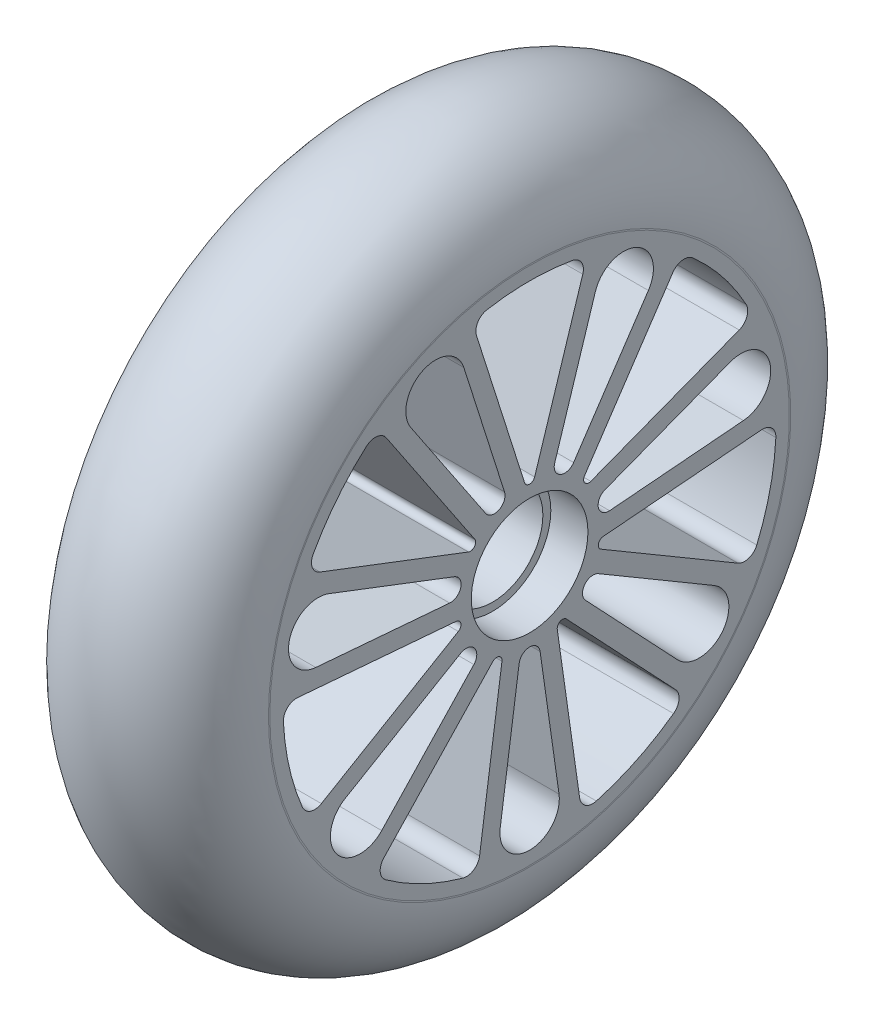
SolidWorks part; units mm, degrees
ref_plane "Front Plane" through (0, 0, 0) normal (0, 0, 1) x (1, 0, 0)
ref_plane "Top Plane" through (0, 0, 0) normal (0, 1, 0) x (1, 0, 0)
ref_plane "Right Plane" through (0, 0, 0) normal (1, 0, 0) x (0, 0, -1)
sketch "Sketch2" plane through (0, 0, 0) normal (0, 0, 1) x (1, 0, 0)
  line L0 (0, -49) -> (0, 49) construction
  line L1 (-14.0194, 46.0581) -> (14.0194, 46.0581)
  line L2 (17.4377, 49.2586) -> (17.4396, 49)
  line L3 (-19.6452, 0) -> (17.4396, 0) construction
  arc A0 (-17.4396, 49) -> (17.4377, 49.2586) centre (0, 49) cw
  arc A1 (-17.4396, 49) -> (-14.0194, 46.0581) centre (-17.4396, 45.5408) cw
  arc A2 (17.4396, 49) -> (14.0194, 46.0581) centre (17.4396, 45.5408) ccw
  point P3 (0, 0)
  point P13 (0, 46.0581)
  dimension "D1" = 98
revolve "Revolve1" add sketch "Sketch2" angle 360 about L3
sketch "Sketch4" plane through (0, 0, 0) normal (0, 0, 1) x (1, 0, 0)
  line L0 (-14.0194, 46.0581) -> (14.0194, 46.0581) construction
  line L1 (-14.0194, 46.0581) -> (14.0194, 46.0581)
  line L2 (-17.4396, 0) -> (-17.4396, 49)
  line L3 (-17.4396, 49) -> (-17.4396, -49) construction
  line L4 (-17.4396, 0) -> (17.4396, 0)
  line L5 (17.4396, 0) -> (17.4396, 49)
  arc A0 (17.4396, 49) -> (14.0194, 46.0581) centre (17.4396, 45.5408) ccw construction
  arc A1 (-14.0194, 46.0581) -> (-17.4396, 49) centre (-17.4396, 45.5408) ccw construction
  arc A2 (17.4396, 49) -> (14.0194, 46.0581) centre (17.4396, 45.5408) ccw
  arc A3 (-14.0194, 46.0581) -> (-17.4396, 49) centre (-17.4396, 45.5408) ccw
revolve "Revolve2" add sketch "Sketch4" angle 360 about L4
sketch "Sketch5" plane through (17.4396, 0, 0) normal (1, 0, 0) x (0, 0, -1)
  line L0 (0, 49.2586) -> (0, -49.2586) construction
  line L1 (-49, 0) -> (49.2586, 0) construction
  circle A0 centre (0, 0) radius 49.2586 construction
  circle A1 centre (0, 0) radius 49 construction
  circle A2 centre (0, 0) radius 11
  dimension "D1" = 22
extrude "Cut-Extrude1" cut sketch "Sketch5" against normal blind 7
mirror "Mirror1" about plane through (0, 0, 0) normal (1, 0, 0) of "Cut-Extrude1"
sketch "Sketch6" plane through (10.4396, 0, 0) normal (1, 0, 0) x (0, 0, -1)
  circle A0 centre (0, 0) radius 9.5
  circle A1 centre (0, 0) radius 11 construction
  dimension "D1" = 1.5
extrude "Cut-Extrude2" cut sketch "Sketch6" against normal through all both and the other way through all
sketch "Sketch7" plane through (17.4396, 0, 0) normal (1, 0, 0) x (0, 0, -1)
  line L0 (0, 0) -> (0, 66.4396) construction
  line L1 (0.9531, 14.0016) -> (10.026, 42.5745)
  line L2 (-0.9531, 14.0016) -> (-10.026, 42.5745)
  line L3 (10.3526, 9.475) -> (27.035, 34.3834)
  line L4 (11.5411, 7.9847) -> (39.5371, 18.7061)
  line L5 (13.8626, -2.1864) -> (43.738, 0.3009)
  line L6 (13.4384, -4.0449) -> (39.276, -19.2483)
  line L7 (6.9338, -12.2014) -> (27.5055, -34.0082)
  line L8 (5.2163, -13.0285) -> (9.4393, -42.7084)
  line L9 (-5.2163, -13.0285) -> (-9.4393, -42.7084)
  line L10 (-6.9338, -12.2014) -> (-27.5055, -34.0082)
  line L11 (-13.4384, -4.0449) -> (-39.276, -19.2483)
  line L12 (-13.8626, -2.1864) -> (-43.738, 0.3009)
  line L13 (-11.5411, 7.9847) -> (-39.5371, 18.7061)
  line L14 (-10.3526, 9.475) -> (-27.035, 34.3834)
  line L15 (10.026, 42.5745) -> (27.035, 34.3834) construction
  line L16 (0.9531, 14.0016) -> (10.3526, 9.475) construction
  line L17 (5.6529, 11.7383) -> (18.5305, 38.4789) construction
  line L18 (18.5305, 38.4789) -> (20.1756, 41.8951) construction
  line L19 (4.7346, 14.3927) -> (12.4028, 38.542)
  line L20 (8.3007, 12.6753) -> (22.4003, 33.7274)
  line L21 (14.2046, 5.2721) -> (37.8663, 14.3337)
  line L22 (15.0854, 1.4132) -> (40.3355, 3.5154)
  line L23 (12.9783, -7.8185) -> (34.8158, -20.6682)
  line L24 (10.5105, -10.9132) -> (27.8972, -29.3438)
  line L25 (1.9791, -15.0216) -> (5.5482, -40.1065)
  line L26 (-1.9791, -15.0216) -> (-5.5482, -40.1065)
  line L27 (-10.5105, -10.9132) -> (-27.8972, -29.3438)
  line L28 (-12.9783, -7.8185) -> (-34.8158, -20.6682)
  line L29 (-15.0854, 1.4132) -> (-40.3355, 3.5154)
  line L30 (-14.2046, 5.2721) -> (-37.8663, 14.3337)
  line L31 (-8.3007, 12.6753) -> (-22.4003, 33.7274)
  line L32 (-4.7346, 14.3927) -> (-12.4028, 38.542)
  circle A0 centre (0, 0) radius 66.4396 construction
  arc A1 (0.9531, 14.0016) -> (-0.9531, 14.0016) centre (0, 14.3042) cw
  circle A2 centre (0, 0) radius 11 construction
  circle A3 centre (0, 0) radius 46.5
  arc A4 (8.0775, 45.7931) -> (-8.0775, 45.7931) centre (0, 0) ccw
  arc A5 (40.8387, 22.2363) -> (30.7662, 34.8667) centre (0, 0) ccw
  arc A7 (10.026, 42.5745) -> (8.0775, 45.7931) centre (7.6432, 43.3311) ccw
  arc A8 (-10.026, 42.5745) -> (-8.0775, 45.7931) centre (-7.6432, 43.3311) cw
  arc A9 (27.035, 34.3834) -> (30.7662, 34.8667) centre (29.1121, 32.9922) cw
  arc A10 (39.5371, 18.7061) -> (40.8387, 22.2363) centre (38.6431, 21.0408) ccw
  arc A11 (11.5411, 7.9847) -> (10.3526, 9.475) centre (11.1835, 8.9185) cw
  arc A12 (42.8475, -18.0649) -> (46.4423, -2.3149) centre (0, 0) ccw
  arc A13 (43.738, 0.3009) -> (46.4423, -2.3149) centre (43.9454, -2.1905) cw
  arc A14 (39.276, -19.2483) -> (42.8475, -18.0649) centre (40.5439, -17.0937) ccw
  arc A15 (13.4384, -4.0449) -> (13.8626, -2.1864) centre (13.9456, -3.183) cw
  arc A16 (12.5913, -44.7628) -> (27.1464, -37.7534) centre (0, 0) ccw
  arc A17 (27.5055, -34.0082) -> (27.1464, -37.7534) centre (25.6869, -35.7237) cw
  arc A18 (9.4393, -42.7084) -> (12.5913, -44.7628) centre (11.9143, -42.3562) ccw
  arc A19 (5.2163, -13.0285) -> (6.9338, -12.2014) centre (6.2064, -12.8877) cw
  arc A20 (-27.1464, -37.7534) -> (-12.5913, -44.7628) centre (0, 0) ccw
  arc A21 (-9.4393, -42.7084) -> (-12.5913, -44.7628) centre (-11.9143, -42.3562) cw
  arc A22 (-27.5055, -34.0082) -> (-27.1464, -37.7534) centre (-25.6869, -35.7237) ccw
  arc A23 (-6.9338, -12.2014) -> (-5.2163, -13.0285) centre (-6.2064, -12.8877) cw
  arc A24 (-46.4423, -2.3149) -> (-42.8475, -18.0649) centre (0, 0) ccw
  arc A25 (-39.276, -19.2483) -> (-42.8475, -18.0649) centre (-40.5439, -17.0937) cw
  arc A26 (-43.738, 0.3009) -> (-46.4423, -2.3149) centre (-43.9454, -2.1905) ccw
  arc A27 (-13.8626, -2.1864) -> (-13.4384, -4.0449) centre (-13.9456, -3.183) cw
  arc A28 (-30.7662, 34.8667) -> (-40.8387, 22.2363) centre (0, 0) ccw
  arc A29 (-39.5371, 18.7061) -> (-40.8387, 22.2363) centre (-38.6431, 21.0408) cw
  arc A30 (-27.035, 34.3834) -> (-30.7662, 34.8667) centre (-29.1121, 32.9922) ccw
  arc A31 (-10.3526, 9.475) -> (-11.5411, 7.9847) centre (-11.1835, 8.9185) cw
  circle A32 centre (0, 0) radius 46.5 construction
  circle A33 centre (0, 0) radius 13.3042 construction
  arc A34 (22.4003, 33.7274) -> (12.4028, 38.542) centre (17.7441, 36.8459) ccw
  arc A35 (4.7346, 14.3927) -> (8.3007, 12.6753) centre (6.6398, 13.7877) ccw
  arc A36 (40.3355, 3.5154) -> (37.8663, 14.3337) centre (39.8706, 9.1002) ccw
  arc A37 (14.2046, 5.2721) -> (15.0854, 1.4132) centre (14.9196, 3.4053) ccw
  arc A38 (27.8972, -29.3438) -> (34.8158, -20.6682) centre (31.9737, -25.4982) ccw
  arc A39 (12.9783, -7.8185) -> (10.5105, -10.9132) centre (11.9646, -9.5414) ccw
  arc A40 (-5.5482, -40.1065) -> (5.5482, -40.1065) centre (0, -40.8959) ccw
  arc A41 (1.9791, -15.0216) -> (-1.9791, -15.0216) centre (0, -15.3032) ccw
  arc A42 (-34.8158, -20.6682) -> (-27.8972, -29.3438) centre (-31.9737, -25.4982) ccw
  arc A43 (-10.5105, -10.9132) -> (-12.9783, -7.8185) centre (-11.9646, -9.5414) ccw
  arc A44 (-37.8663, 14.3337) -> (-40.3355, 3.5154) centre (-39.8706, 9.1002) ccw
  arc A45 (-15.0854, 1.4132) -> (-14.2046, 5.2721) centre (-14.9196, 3.4053) ccw
  arc A46 (-12.4028, 38.542) -> (-22.4003, 33.7274) centre (-17.7441, 36.8459) ccw
  arc A47 (-8.3007, 12.6753) -> (-4.7346, 14.3927) centre (-6.6398, 13.7877) ccw
  point P18 (0, 11)
  point P20 (10.8638, 45.2131)
  point P23 (-10.8638, 45.2131)
  point P77 (0, 0)
  point P125 (0, 0)
  dimension "D3" = 1
  dimension "D4" = 2.5
  dimension "D5" = 7
  dimension "D1" = 2.5
  dimension "D2" = 7
extrude "Cut-Extrude3" cut sketch "Sketch7" against normal through all both
